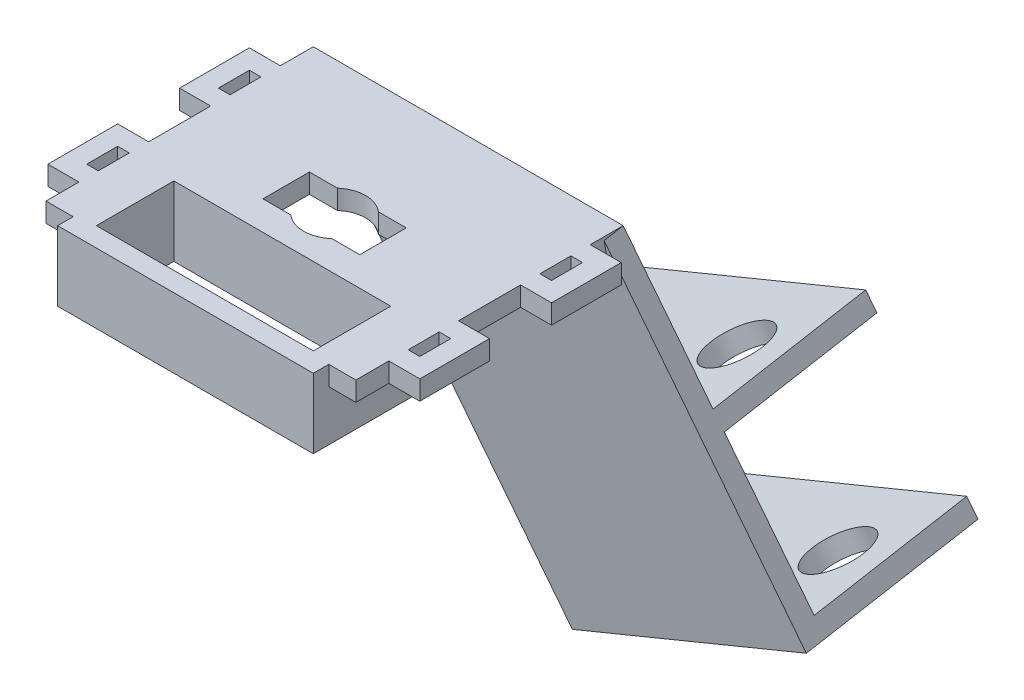
SolidWorks part; units mm, degrees
ref_plane "Front Plane" through (0, 0, 0) normal (0, 0, 1) x (1, 0, 0)
ref_plane "Top Plane" through (0, 0, 0) normal (0, 1, 0) x (1, 0, 0)
ref_plane "Right Plane" through (0, 0, 0) normal (1, 0, 0) x (0, 0, -1)
sketch "Sketch1" plane through (0, 0, 0) normal (0, 1, 0) x (1, 0, 0)
  line L1 (-7.9375, 3.81) -> (7.9375, 3.81)
  line L2 (-7.9375, 3.81) -> (-7.9375, -3.81)
  line L3 (-7.9375, -3.81) -> (7.9375, -3.81)
  line L4 (7.9375, 3.81) -> (7.9375, -3.81)
  line L5 (-25.4, 21.9075) -> (25.4, 21.9075)
  line L6 (-25.4, 21.9075) -> (-25.4, -21.9075)
  line L7 (-25.4, -21.9075) -> (25.4, -21.9075)
  line L8 (25.4, 21.9075) -> (25.4, -21.9075)
  line L9 (-17.78, -8.5725) -> (17.78, -8.5725)
  line L10 (-17.78, -8.5725) -> (-17.78, -13.6525)
  line L11 (-17.78, -13.6525) -> (17.78, -13.6525)
  line L12 (17.78, -8.5725) -> (17.78, -13.6525)
  point P4 (0, 3.81)
  point P6 (-7.9375, 0)
  point P11 (0, 21.9075)
  point P12 (25.4, 0)
  point P17 (0, -8.5725)
  dimension "D1" = 7.62
  dimension "D2" = 15.875
  dimension "D3" = 43.815
  dimension "D4" = 50.8
  dimension "D5" = 8.255
  dimension "D6" = 5.08
  dimension "D7" = 35.56
extrude "Boss-Extrude1" add sketch "Sketch1" along normal blind 3.175
sketch "Sketch2" plane through (0, 3.175, 0) normal (0, 1, 0) x (1, 0, 0)
  line L0 (-25.4, -21.9075) -> (25.4, -21.9075) construction
  line L1 (25.4, -21.9075) -> (25.4, 21.9075) construction
  line L2 (25.4, 21.9075) -> (-25.4, 21.9075) construction
  line L3 (-25.4, 21.9075) -> (-25.4, -21.9075) construction
  line L4 (-25.4, -21.9075) -> (25.4, -21.9075)
  line L5 (25.4, -21.9075) -> (25.4, 21.9075)
  line L6 (25.4, 21.9075) -> (-25.4, 21.9075)
  line L7 (-25.4, 21.9075) -> (-25.4, -21.9075)
  line L8 (-22.225, 18.7325) -> (-22.225, -18.7325)
  line L9 (-22.225, -18.7325) -> (22.225, -18.7325)
  line L10 (22.225, -18.7325) -> (22.225, 18.7325)
  line L11 (22.225, 18.7325) -> (-22.225, 18.7325)
  dimension "D1" = 3.175
extrude "Boss-Extrude2" add sketch "Sketch2" along normal blind 8.255
sketch "Sketch3" plane through (0, 11.43, 0) normal (0, 1, 0) x (1, 0, 0)
  line L0 (-20.955, -21.9075) -> (-20.955, -24.4475)
  line L1 (-25.4, -21.9075) -> (25.4, -21.9075) construction
  line L2 (-20.955, -24.4475) -> (20.955, -24.4475)
  line L3 (20.955, -24.4475) -> (20.955, -21.9075)
  line L4 (20.955, -21.9075) -> (-20.955, -21.9075)
  line L5 (-17.78, -8.5725) -> (-17.78, -13.6525) construction
  point P8 (0, -21.9075)
  dimension "D1" = 3.175
  dimension "D2" = 2.54
extrude "Boss-Extrude3" add sketch "Sketch3" against normal up to surface (11.43 mm away) up to face at (0, 0, 0)
sketch "Sketch4" plane through (0, 11.43, 0) normal (0, 1, 0) x (1, 0, 0)
  line L0 (-22.225, -18.7325) -> (22.225, -18.7325) construction
  line L1 (-17.78, -18.7325) -> (17.78, -18.7325)
  line L2 (-17.78, -18.7325) -> (-17.78, -21.2725)
  line L3 (-17.78, -21.2725) -> (17.78, -21.2725)
  line L4 (17.78, -18.7325) -> (17.78, -21.2725)
  line L5 (-17.78, -8.5725) -> (-17.78, -13.6525) construction
  line L6 (17.78, -13.6525) -> (17.78, -8.5725) construction
  line L7 (-20.955, -24.4475) -> (20.955, -24.4475) construction
  dimension "D1" = 3.175
extrude "Cut-Extrude1" cut sketch "Sketch4" against normal up to surface (8.255 mm away) up to face at (0, 3.175, 0)
sketch "Sketch5" plane through (0, 11.43, 0) normal (0, 1, 0) x (1, 0, 0)
  line L0 (-25.4, -16.51) -> (-30.48, -16.51)
  line L1 (-25.4, 21.9075) -> (-25.4, -21.9075) construction
  line L2 (-30.48, -16.51) -> (-30.48, -5.08)
  line L3 (-30.48, -5.08) -> (-25.4, -5.08)
  line L4 (-25.4, -5.08) -> (-25.4, -8.255)
  line L5 (-25.4, -8.255) -> (-27.305, -8.255)
  line L6 (-27.305, -8.255) -> (-27.305, -13.335)
  line L7 (-27.305, -13.335) -> (-25.4, -13.335)
  line L8 (-25.4, -13.335) -> (-25.4, -16.51)
  line L9 (-25.4, -21.9075) -> (-20.955, -21.9075) construction
  dimension "D1" = 5.3975
  dimension "D2" = 1.905
  dimension "D3" = 5.08
  dimension "D4" = 3.175
  dimension "D5" = 3.175
extrude "Boss-Extrude4" add sketch "Sketch5" against normal blind 3.175
mirror "Mirror1" about plane through (0, 0, 0) normal (0, 0, 1) of "Boss-Extrude4"
mirror "Mirror2" about plane through (0, 0, 0) normal (1, 0, 0) of "Mirror1", "Boss-Extrude4"
sketch "Sketch7" plane through (0, 3.175, 0) normal (0, 1, 0) x (1, 0, 0)
  line L0 (-22.225, -18.7325) -> (-17.78, -18.7325)
  line L1 (-17.78, -18.7325) -> (-17.78, -8.5725)
  line L2 (-17.78, -8.5725) -> (17.78, -8.5725)
  line L3 (17.78, -8.5725) -> (17.78, -18.7325)
  line L4 (17.78, -18.7325) -> (22.225, -18.7325)
  line L5 (22.225, -18.7325) -> (22.225, 18.7325)
  line L6 (22.225, 18.7325) -> (-22.225, 18.7325)
  line L7 (-22.225, 18.7325) -> (-22.225, -18.7325)
  line L9 (-7.9375, 3.81) -> (7.9375, 3.81)
  line L10 (-7.9375, 3.81) -> (-7.9375, -3.81)
  line L11 (-7.9375, -3.81) -> (7.9375, -3.81)
  line L12 (7.9375, 3.81) -> (7.9375, -3.81)
extrude "Boss-Extrude5" add sketch "Sketch7" along normal up to surface (8.255 mm away) up to face at (26.3525, 11.43, -10.795)
sketch "Sketch8" plane through (0, 11.43, 0) normal (0, 1, 0) x (1, 0, 0)
  line L0 (-25.4, 21.9075) -> (-25.4, -21.9075)
  line L1 (-25.4, -16.51) -> (-25.4, -21.9075) construction
  line L2 (-25.4, -21.9075) -> (-20.955, -21.9075)
  line L3 (-20.955, -21.9075) -> (-20.955, -5.3975)
  line L4 (-20.955, -5.3975) -> (20.955, -5.3975)
  line L5 (20.955, -5.3975) -> (20.955, -21.9075)
  line L6 (20.955, -21.9075) -> (25.4, -21.9075)
  line L7 (25.4, -21.9075) -> (25.4, -16.51) construction
  line L8 (25.4, -21.9075) -> (25.4, 21.9075)
  line L9 (25.4, 21.9075) -> (-25.4, 21.9075)
  line L11 (-17.78, -8.5725) -> (17.78, -8.5725) construction
  dimension "D2" = 3.175
extrude "Cut-Extrude2" cut sketch "Sketch8" along normal up to surface (8.255 mm away) from surface
ref_plane "Plane1" through (0, 4.0911, -23.2016) normal (0, 0.1736, -0.9848) x (-1, 0, 0)
sketch "Sketch10" plane through (0, 4.0911, -23.2016) normal (0, 0.1736, -0.9848) x (-1, 0, 0)
  line L0 (-25.4, 7.4522) -> (-36.1345, -15.5681)
  line L1 (-36.1345, -15.5681) -> (5.5923, -35.0256)
  line L2 (5.5923, -35.0256) -> (25.4, 7.4522)
  line L3 (25.4, 7.4522) -> (-25.4, 7.4522)
  line L4 (-25.4, 7.4522) -> (-25.4, 4.3254) construction
  dimension "D1" = 25
  dimension "D2" = 25.4
extrude "Boss-Extrude6" add sketch "Sketch10" against normal blind 3.175
sketch "Sketch11" plane through (23.7177, 10.8917, 1.9205) normal (0.9063, 0.4162, 0.0734) x (0.0667, 0.0306, -0.9973)
  line L0 (24.7654, -25.7957) -> (29.7757, -57.1479)
  line L1 (29.7757, -57.1479) -> (57.9927, -52.6386)
  line L2 (57.9927, -52.6386) -> (57.4917, -49.5034)
  line L3 (57.4917, -49.5034) -> (32.4099, -53.5116)
  line L4 (32.4099, -53.5116) -> (28.4017, -28.4299)
  line L5 (28.4017, -28.4299) -> (53.4834, -24.4216)
  line L6 (53.4834, -24.4216) -> (52.9824, -21.2864)
  line L7 (52.9824, -21.2864) -> (24.7654, -25.7957)
  line L8 (23.8924, -0.2129) -> (27.9007, -25.2946) construction
  dimension "D1" = 3.175
  dimension "D2" = 25.4
  dimension "D3" = 25.4
extrude "Boss-Extrude7" add sketch "Sketch11" against normal up to surface (46.0404 mm away) up to face at (-16.9369, -6.6832, -23.6998)
sketch "Sketch12" plane through (12.4168, -26.2233, -4.6239) normal (-0.4226, 0.8925, 0.1574) x (0.9063, 0.4162, 0.0734)
  line L0 (-19.8708, 48.9595) -> (-19.8708, 23.5595) construction
  line L1 (-9.5506, 36.2595) -> (15.8494, 36.2595) construction
  line L2 (-19.8708, 48.9595) -> (26.1696, 48.9595) construction
  circle A0 centre (-9.5506, 36.2595) radius 5.08
  circle A1 centre (15.8494, 36.2595) radius 5.08
  point P7 (-19.8708, 36.2595)
  point P9 (3.1494, 48.9595)
  point P10 (3.1494, 36.2595)
  dimension "D2" = 10.16
  dimension "D1" = 25.4
extrude "Cut-Extrude3" cut sketch "Sketch12" against normal through all
sketch "Sketch13" plane through (0, 11.43, 0) normal (0, 1, 0) x (1, 0, 0)
  circle A0 centre (0, 0) radius 5.08
  dimension "D1" = 10.16
extrude "Cut-Extrude4" cut sketch "Sketch13" against normal through all
